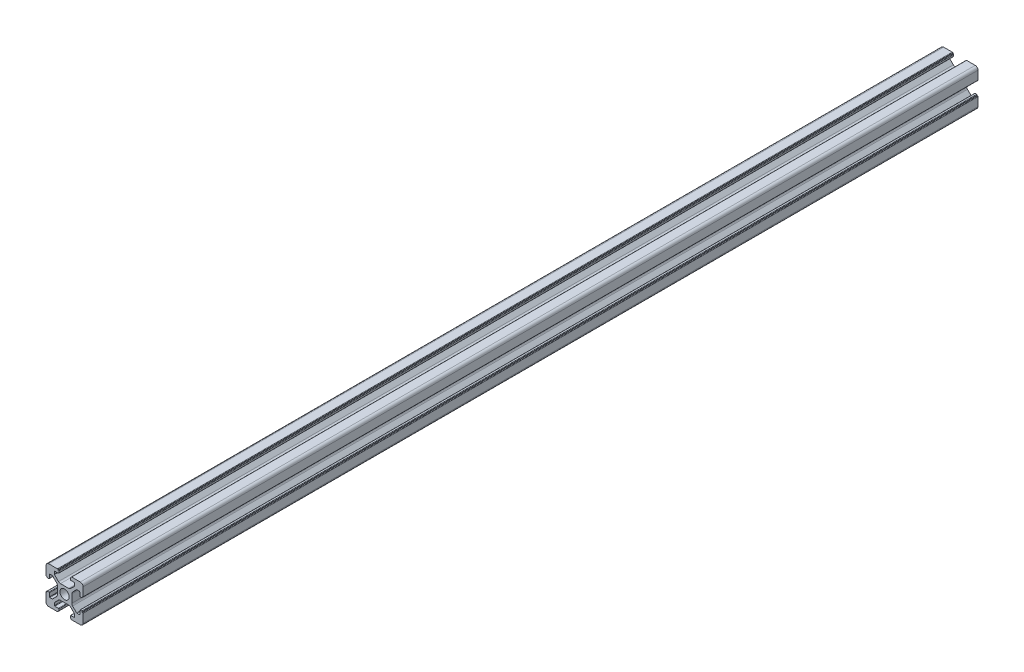
SolidWorks part; units mm, degrees
material "1060 Alloy"
ref_plane "前视基准面" through (0, 0, 0) normal (0, 0, 1) x (1, 0, 0)
ref_plane "上视基准面" through (0, 0, 0) normal (0, 1, 0) x (1, 0, 0)
ref_plane "右视基准面" through (0, 0, 0) normal (1, 0, 0) x (0, 0, -1)
sketch "草图1" plane through (0, 0, 0) normal (0, 0, 1) x (1, 0, 0)
  line L0 (0, 0) -> (0, 5.5) construction
  line L1 (-8.5023, -10.0023) -> (-3.85, -10.0023)
  line L2 (-10.0023, -8.5023) -> (-10.0023, -3.85)
  line L3 (-8.5023, 10.0023) -> (-3.85, 10.0023)
  line L4 (10.0023, -8.5023) -> (10.0023, -3.85)
  line L5 (-10.0023, -10.0023) -> (10.0023, 10.0023) construction
  line L6 (-10.0023, 10.0023) -> (10.0023, -10.0023) construction
  line L7 (-2.218, -3.9) -> (2.218, -3.9)
  line L8 (-3.9, -2.218) -> (-3.9, 2.218)
  line L9 (-2.218, 3.9) -> (2.218, 3.9)
  line L10 (3.9, -2.218) -> (3.9, 2.218)
  line L11 (-3.9, -3.9) -> (3.9, 3.9) construction
  line L12 (-3.9, 3.9) -> (3.9, -3.9) construction
  line L13 (-5.25, -8.2) -> (-3.35, -8.2)
  line L14 (-8.2, -5.25) -> (-8.2, -3.35)
  line L15 (-5.25, 8.2) -> (-3.35, 8.2)
  line L16 (8.2, -5.25) -> (8.2, -3.35)
  line L17 (-8.2, -8.2) -> (8.2, 8.2) construction
  line L18 (-8.2, 8.2) -> (8.2, -8.2) construction
  line L19 (-7.95, 5.5) -> (-6.6642, 5.5)
  line L20 (0, 0) -> (5.5, 0) construction
  line L23 (-5.5, 7.95) -> (-5.5, 6.6642)
  line L26 (0, 0) -> (-0.5303, 0.5303)
  line L27 (3.2787, 4.3393) -> (5.4268, 6.4874)
  line L28 (0, 0) -> (0.5303, -0.5303)
  line L29 (5.5, 6.6642) -> (5.5, 7.95)
  line L30 (4.3393, 3.2787) -> (6.4874, 5.4268)
  line L31 (6.6642, 5.5) -> (7.95, 5.5)
  line L32 (4.3393, -3.2787) -> (6.4874, -5.4268)
  line L33 (3.2787, -4.3393) -> (5.4268, -6.4874)
  line L34 (-3.2787, -4.3393) -> (-5.4268, -6.4874)
  line L35 (-4.3393, -3.2787) -> (-6.4874, -5.4268)
  line L36 (-4.3393, 3.2787) -> (-6.4874, 5.4268)
  line L37 (-3.2787, 4.3393) -> (-5.4268, 6.4874)
  line L38 (3.1, -8.45) -> (3.1, -9.2523)
  line L39 (8.45, 3.1) -> (9.2523, 3.1)
  line L40 (-5.5, -6.6642) -> (-5.5, -7.95)
  line L41 (-6.6642, -5.5) -> (-7.95, -5.5)
  line L42 (5.5, -6.6642) -> (5.5, -7.95)
  line L43 (6.6642, -5.5) -> (7.95, -5.5)
  line L44 (9.2523, -3.1) -> (8.45, -3.1)
  line L46 (10.0023, 3.85) -> (10.0023, 8.5023)
  line L47 (8.2, 3.35) -> (8.2, 5.25)
  line L48 (-3.1, -9.2523) -> (-3.1, -8.45)
  line L49 (-8.45, -3.1) -> (-9.2523, -3.1)
  line L50 (-9.2523, 3.1) -> (-8.45, 3.1)
  line L51 (-3.1, 8.45) -> (-3.1, 9.2523)
  line L52 (3.1, 9.2523) -> (3.1, 8.45)
  line L53 (3.85, 10.0023) -> (8.5023, 10.0023)
  line L54 (3.35, 8.2) -> (5.25, 8.2)
  line L55 (-10.0023, 3.85) -> (-10.0023, 8.5023)
  line L56 (-8.2, 3.35) -> (-8.2, 5.25)
  line L57 (3.35, -8.2) -> (5.25, -8.2)
  line L58 (3.85, -10.0023) -> (8.5023, -10.0023)
  line L59 (9.7523, -3.6) -> (9.5023, -3.6)
  line L61 (9.7523, 3.6) -> (9.5023, 3.6)
  line L62 (9.5023, -3.6) -> (9.5023, -3.35)
  line L63 (3.6, -9.7523) -> (3.6, -9.5023)
  line L64 (3.35, -9.5023) -> (3.6, -9.5023)
  line L65 (9.5023, 3.35) -> (9.5023, 3.6)
  line L66 (-3.6, -9.5023) -> (-3.35, -9.5023)
  line L67 (-3.6, -9.7523) -> (-3.6, -9.5023)
  line L68 (-9.7523, -3.6) -> (-9.5023, -3.6)
  line L69 (-9.5023, -3.35) -> (-9.5023, -3.6)
  line L70 (-9.5023, 3.6) -> (-9.5023, 3.35)
  line L71 (-9.7523, 3.6) -> (-9.5023, 3.6)
  line L72 (-3.6, 9.7523) -> (-3.6, 9.5023)
  line L73 (-3.35, 9.5023) -> (-3.6, 9.5023)
  line L74 (3.6, 9.5023) -> (3.35, 9.5023)
  line L75 (3.6, 9.7523) -> (3.6, 9.5023)
  circle A0 centre (0, 0) radius 2.5
  arc A1 (10.0023, 8.5023) -> (8.5023, 10.0023) centre (8.5023, 8.5023) ccw
  arc A2 (8.5023, -10.0023) -> (10.0023, -8.5023) centre (8.5023, -8.5023) ccw
  arc A3 (-10.0023, -8.5023) -> (-8.5023, -10.0023) centre (-8.5023, -8.5023) ccw
  arc A4 (-10.0023, 8.5023) -> (-8.5023, 10.0023) centre (-8.5023, 8.5023) cw
  arc A5 (-9.5023, -3.35) -> (-9.2523, -3.1) centre (-9.2523, -3.35) cw
  arc A6 (-9.7523, -3.6) -> (-10.0023, -3.85) centre (-9.7523, -3.85) ccw
  arc A7 (-8.45, -3.1) -> (-8.2, -3.35) centre (-8.45, -3.35) cw
  arc A8 (-7.95, -5.5) -> (-8.2, -5.25) centre (-7.95, -5.25) cw
  arc A9 (-6.4874, -5.4268) -> (-6.6642, -5.5) centre (-6.6642, -5.25) cw
  arc A10 (-5.4268, -6.4874) -> (-5.5, -6.6642) centre (-5.25, -6.6642) ccw
  arc A11 (-5.5, -7.95) -> (-5.25, -8.2) centre (-5.25, -7.95) ccw
  arc A12 (-3.6, -9.7523) -> (-3.85, -10.0023) centre (-3.85, -9.7523) cw
  arc A13 (-3.35, -9.5023) -> (-3.1, -9.2523) centre (-3.35, -9.2523) ccw
  arc A14 (-3.1, -8.45) -> (-3.35, -8.2) centre (-3.35, -8.45) ccw
  arc A15 (3.1, -8.45) -> (3.35, -8.2) centre (3.35, -8.45) cw
  arc A16 (5.5, -7.95) -> (5.25, -8.2) centre (5.25, -7.95) cw
  arc A17 (5.4268, -6.4874) -> (5.5, -6.6642) centre (5.25, -6.6642) cw
  arc A18 (6.4874, -5.4268) -> (6.6642, -5.5) centre (6.6642, -5.25) ccw
  arc A19 (7.95, -5.5) -> (8.2, -5.25) centre (7.95, -5.25) ccw
  arc A20 (8.45, -3.1) -> (8.2, -3.35) centre (8.45, -3.35) ccw
  arc A21 (9.5023, -3.35) -> (9.2523, -3.1) centre (9.2523, -3.35) ccw
  arc A22 (9.7523, -3.6) -> (10.0023, -3.85) centre (9.7523, -3.85) cw
  arc A23 (3.35, -9.5023) -> (3.1, -9.2523) centre (3.35, -9.2523) cw
  arc A24 (3.6, -9.7523) -> (3.85, -10.0023) centre (3.85, -9.7523) ccw
  arc A25 (7.95, 5.5) -> (8.2, 5.25) centre (7.95, 5.25) cw
  arc A26 (8.2, 3.35) -> (8.45, 3.1) centre (8.45, 3.35) ccw
  arc A27 (9.5023, 3.35) -> (9.2523, 3.1) centre (9.2523, 3.35) cw
  arc A28 (9.7523, 3.6) -> (10.0023, 3.85) centre (9.7523, 3.85) ccw
  arc A29 (6.6642, 5.5) -> (6.4874, 5.4268) centre (6.6642, 5.25) ccw
  arc A30 (5.4268, 6.4874) -> (5.5, 6.6642) centre (5.25, 6.6642) ccw
  arc A31 (5.5, 7.95) -> (5.25, 8.2) centre (5.25, 7.95) ccw
  arc A32 (3.1, 8.45) -> (3.35, 8.2) centre (3.35, 8.45) ccw
  arc A33 (3.6, 9.7523) -> (3.85, 10.0023) centre (3.85, 9.7523) cw
  arc A34 (3.35, 9.5023) -> (3.1, 9.2523) centre (3.35, 9.2523) ccw
  arc A35 (-9.7523, 3.6) -> (-10.0023, 3.85) centre (-9.7523, 3.85) cw
  arc A36 (-9.5023, 3.35) -> (-9.2523, 3.1) centre (-9.2523, 3.35) ccw
  arc A37 (-8.45, 3.1) -> (-8.2, 3.35) centre (-8.45, 3.35) ccw
  arc A38 (-8.2, 5.25) -> (-7.95, 5.5) centre (-7.95, 5.25) cw
  arc A39 (-6.4874, 5.4268) -> (-6.6642, 5.5) centre (-6.6642, 5.25) ccw
  arc A40 (-5.4268, 6.4874) -> (-5.5, 6.6642) centre (-5.25, 6.6642) cw
  arc A41 (-5.5, 7.95) -> (-5.25, 8.2) centre (-5.25, 7.95) cw
  arc A42 (-3.1, 8.45) -> (-3.35, 8.2) centre (-3.35, 8.45) cw
  arc A43 (-3.1, 9.2523) -> (-3.35, 9.5023) centre (-3.35, 9.2523) ccw
  arc A44 (-3.6, 9.7523) -> (-3.85, 10.0023) centre (-3.85, 9.7523) ccw
  arc A45 (-4.3393, 3.2787) -> (-3.9, 2.218) centre (-5.4, 2.218) cw
  arc A46 (-3.2787, 4.3393) -> (-2.218, 3.9) centre (-2.218, 5.4) ccw
  arc A47 (3.2787, 4.3393) -> (2.218, 3.9) centre (2.218, 5.4) cw
  arc A48 (4.3393, 3.2787) -> (3.9, 2.218) centre (5.4, 2.218) ccw
  arc A49 (4.3393, -3.2787) -> (3.9, -2.218) centre (5.4, -2.218) cw
  arc A50 (3.2787, -4.3393) -> (2.218, -3.9) centre (2.218, -5.4) ccw
  arc A51 (-4.3393, -3.2787) -> (-3.9, -2.218) centre (-5.4, -2.218) ccw
  arc A52 (-2.218, -3.9) -> (-3.2787, -4.3393) centre (-2.218, -5.4) ccw
  point P0 (0, 0)
  point P7 (10.0023, 0)
  point P62 (0, 0)
  point P76 (0, 0)
  point P92 (-8.2, -5.5)
  point P99 (0, 0)
  point P106 (-5.5, -8.2)
  point P117 (5.5, -8.2)
  point P124 (8.2, -5.5)
  point P137 (8.2, 5.5)
  point P140 (8.2, 3.1)
  point P147 (6.5607, 5.5)
  point P152 (5.5, 8.2)
  point P167 (-8.2, 5.5)
  point P174 (-5.5, 8.2)
  dimension "D1" = 1.5
  dimension "D5" = 0.25
  dimension "D6" = 1.5
  dimension "D2" = 4
  dimension "D3" = 4
  dimension "D4" = 4
extrude "凸台-拉伸1" add sketch "草图1" along normal blind 482.6 contours A52 L7 A50 L33 A17 L42 A16 L57 A15 L38 A23 L64 L63 A24 L58 A2 L4 A22 L59 L62 A21 L44 A20 L16 A19 L43 A18 L32 A49 L10 A48 L30 A29 L31 A25 L47 A26 L39 A27 L65 L61 A28 L46 A1 L53 A33 L75 L74 A34 L52 A32
ref_plane "Plane1" through (0, 0, 241.3) normal (0, 0, 1) x (1, 0, 0)
